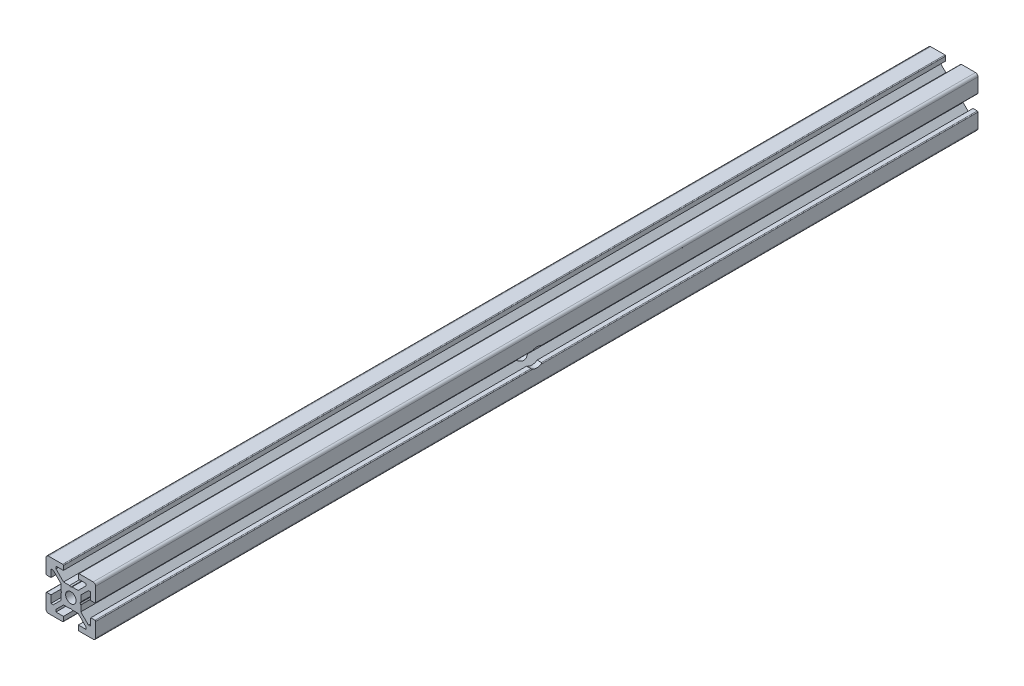
SolidWorks part; units mm, degrees
ref_plane "Front Plane" through (0, 0, 0) normal (0, 0, 1) x (1, 0, 0)
ref_plane "Top Plane" through (0, 0, 0) normal (0, 1, 0) x (1, 0, 0)
ref_plane "Right Plane" through (0, 0, 0) normal (1, 0, 0) x (0, 0, -1)
ref_plane "Plane1" through (0, 0, 0) normal (0, 0, 1) x (1, 0, 0)
sketch "Sketch1" plane through (0, 0, 0) normal (0, 0, 1) x (1, 0, 0)
  line L0 (-10, 9) -> (-10, 3.3)
  line L1 (-9.7, 3) -> (-8, 3)
  line L2 (-8, 3) -> (-8, 6)
  line L3 (-8, 6) -> (-7.0607, 6)
  line L4 (-7.0607, 6) -> (-4, 2.9393)
  line L5 (-4, 2.9393) -> (-4, 0.5196)
  line L6 (-4, 0.5196) -> (-3.7, 0)
  line L7 (-3.7, 0) -> (-4, -0.5196)
  line L8 (-4, -0.5196) -> (-4, -2.9393)
  line L9 (-4, -2.9393) -> (-7.0607, -6)
  line L10 (-7.0607, -6) -> (-8, -6)
  line L11 (-8, -6) -> (-8, -3)
  line L12 (-8, -3) -> (-9.7, -3)
  line L13 (-10, -3.3) -> (-10, -9)
  line L14 (-9, -10) -> (-3.3, -10)
  line L15 (-3, -9.7) -> (-3, -8)
  line L16 (-3, -8) -> (-6, -8)
  line L17 (-6, -8) -> (-6, -7.0607)
  line L18 (-6, -7.0607) -> (-2.9393, -4)
  line L19 (-2.9393, -4) -> (-0.5196, -4)
  line L20 (-0.5196, -4) -> (0, -3.7)
  line L21 (0, -3.7) -> (0.5196, -4)
  line L22 (0.5196, -4) -> (2.9393, -4)
  line L23 (2.9393, -4) -> (6, -7.0607)
  line L24 (6, -7.0607) -> (6, -8)
  line L25 (6, -8) -> (3, -8)
  line L26 (3, -8) -> (3, -9.7)
  line L27 (3.3, -10) -> (9, -10)
  line L28 (10, -9) -> (10, -3.3)
  line L29 (9.7, -3) -> (8, -3)
  line L30 (8, -3) -> (8, -6)
  line L31 (8, -6) -> (7.0606, -6)
  line L32 (7.0606, -6) -> (4, -2.9393)
  line L33 (4, -2.9393) -> (4, -0.5196)
  line L34 (4, -0.5196) -> (3.7, 0)
  line L35 (3.7, 0) -> (4, 0.5196)
  line L36 (4, 0.5196) -> (4, 2.9393)
  line L37 (4, 2.9393) -> (7.0607, 6)
  line L38 (7.0607, 6) -> (8, 6)
  line L39 (8, 6) -> (8, 3)
  line L40 (8, 3) -> (9.7, 3)
  line L41 (10, 3.3) -> (10, 9)
  line L42 (9, 10) -> (3.3, 10)
  line L43 (3, 9.7) -> (3, 8)
  line L44 (3, 8) -> (6, 8)
  line L45 (6, 8) -> (6, 7.0607)
  line L46 (6, 7.0607) -> (2.9393, 4)
  line L47 (2.9393, 4) -> (0.5196, 4)
  line L48 (0.5196, 4) -> (0, 3.7)
  line L49 (0, 3.7) -> (-0.5196, 4)
  line L50 (-0.5196, 4) -> (-2.9394, 4)
  line L51 (-2.9394, 4) -> (-6, 7.0606)
  line L52 (-6, 7.0606) -> (-6, 8)
  line L53 (-6, 8) -> (-3, 8)
  line L54 (-3, 8) -> (-3, 9.7)
  line L55 (-3.3, 10) -> (-9, 10)
  arc A0 (-10, 3.3) -> (-9.7, 3) centre (-9.7, 3.3) ccw
  arc A1 (-9.7, -3) -> (-10, -3.3) centre (-9.7, -3.3) ccw
  arc A2 (-10, -9) -> (-9, -10) centre (-9, -9) ccw
  arc A3 (-3.3, -10) -> (-3, -9.7) centre (-3.3, -9.7) ccw
  arc A4 (3, -9.7) -> (3.3, -10) centre (3.3, -9.7) ccw
  arc A5 (9, -10) -> (10, -9) centre (9, -9) ccw
  arc A6 (10, -3.3) -> (9.7, -3) centre (9.7, -3.3) ccw
  arc A7 (9.7, 3) -> (10, 3.3) centre (9.7, 3.3) ccw
  arc A8 (10, 9) -> (9, 10) centre (9, 9) ccw
  arc A9 (3.3, 10) -> (3, 9.7) centre (3.3, 9.7) ccw
  arc A10 (-3, 9.7) -> (-3.3, 10) centre (-3.3, 9.7) ccw
  arc A11 (-9, 10) -> (-10, 9) centre (-9, 9) ccw
extrude "Boss-Extrude1" add sketch "Sketch1" against normal blind 355
ref_plane "Plane2" through (0, 0, 0) normal (1, 0, 0) x (0, 0, -1)
sketch "Sketch2" plane through (0, 0, 0) normal (1, 0, 0) x (0, 0, -1)
  line L0 (0, 0) -> (0, 2.1)
  line L1 (0, 2.1) -> (355, 2.1)
  line L2 (355, 2.1) -> (355, 0)
  line L3 (355, 0) -> (0, 0)
  line L4 (355, 0) -> (0, 0) construction
revolve "Cut-Revolve1" cut sketch "Sketch2" angle 360 about L4
ref_plane "Plane3" through (0, 0, 0) normal (1, 0, 0) x (0, 0, -1)
sketch "Sketch3" plane through (0, 0, 0) normal (1, 0, 0) x (0, 0, -1)
  circle A0 centre (177.5, 0) radius 3.6751
extrude "Cut-Extrude1" cut sketch "Sketch3" against normal blind 10 and the other way blind 10
